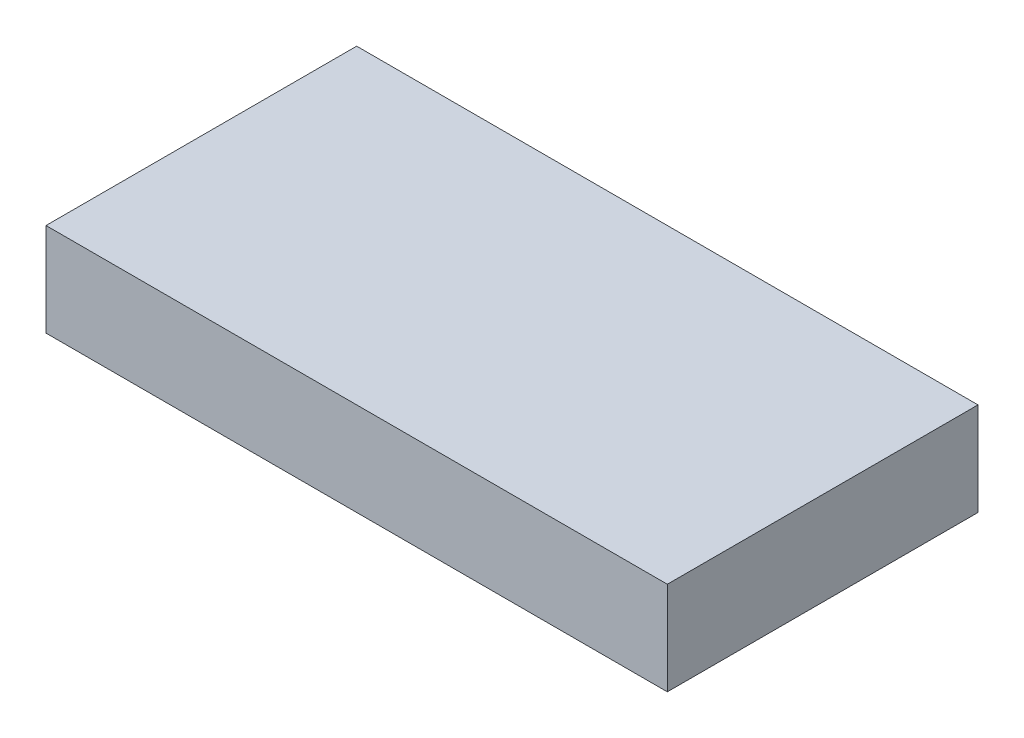
SolidWorks part; units mm, degrees
ref_plane "Front Plane" through (0, 0, 0) normal (0, 0, 1) x (1, 0, 0)
ref_plane "Top Plane" through (0, 0, 0) normal (0, 1, 0) x (1, 0, 0)
ref_plane "Right Plane" through (0, 0, 0) normal (1, 0, 0) x (0, 0, -1)
sketch "Sketch1" plane through (0, 0, 0) normal (0, 1, 0) x (1, 0, 0)
  line L1 (-5.08, -2.54) -> (5.08, -2.54)
  line L2 (-5.08, -2.54) -> (-5.08, 2.54)
  line L3 (-5.08, 2.54) -> (5.08, 2.54)
  line L4 (5.08, -2.54) -> (5.08, 2.54)
  line L5 (-5.08, -2.54) -> (5.08, 2.54) construction
  line L6 (-5.08, 2.54) -> (5.08, -2.54) construction
  point P0 (0, 0)
  dimension "D1" = 5.08
  dimension "D2" = 10.16
extrude "Boss-Extrude1" add sketch "Sketch1" along normal blind 1.524
